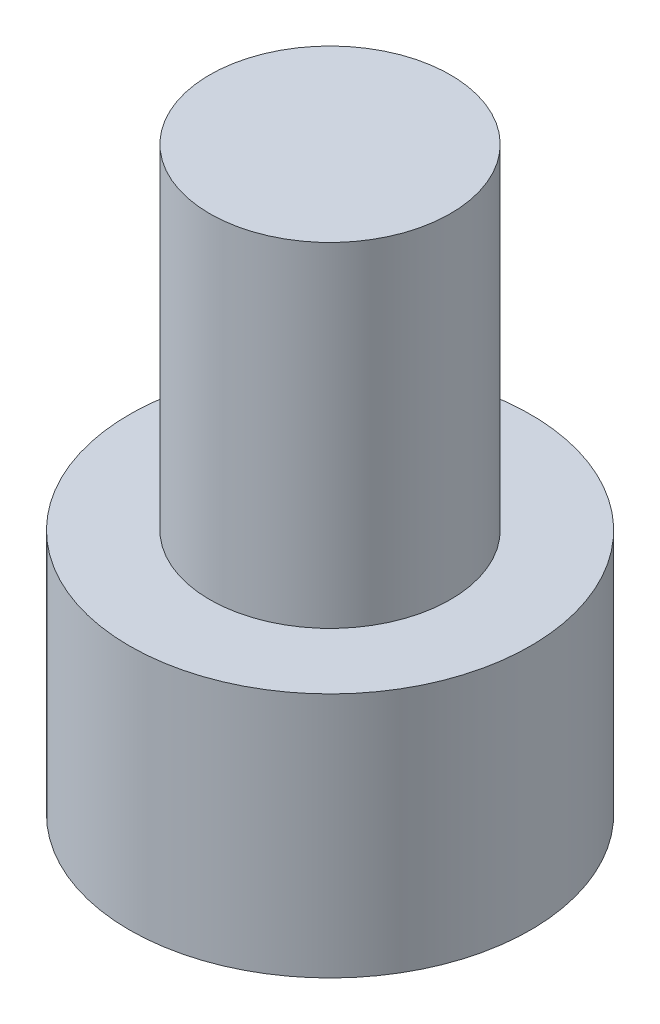
SolidWorks part; units mm, degrees
ref_plane "Front Plane" through (0, 0, 0) normal (0, 0, 1) x (1, 0, 0)
ref_plane "Top Plane" through (0, 0, 0) normal (0, 1, 0) x (1, 0, 0)
ref_plane "Right Plane" through (0, 0, 0) normal (1, 0, 0) x (0, 0, -1)
sketch "Sketch1" plane through (0, 0, 0) normal (0, 1, 0) x (1, 0, 0)
  circle A0 centre (0, 0) radius 2.8575
  dimension "D1" = 5.715
extrude "Boss-Extrude1" add sketch "Sketch1" along normal blind 3.5052
sketch "Sketch2" plane through (0, 0, 0) normal (0, -1, 0) x (1, 0, 0)
  line L1 (1.604, 0) -> (0.802, 1.3891)
  line L2 (0.802, 1.3891) -> (-0.802, 1.3891)
  line L3 (-0.802, 1.3891) -> (-1.604, 0)
  line L4 (-1.604, 0) -> (-0.802, -1.3891)
  line L5 (-0.802, -1.3891) -> (0.802, -1.3891)
  line L6 (0.802, -1.3891) -> (1.604, 0)
  circle A0 centre (0, 0) radius 1.3891 construction
  dimension "D1" = 2.7781
extrude "Cut-Extrude1" cut sketch "Sketch2" against normal blind 1.9558
sketch "Sketch3" plane through (0, 3.5052, 0) normal (0, 1, 0) x (1, 0, 0)
  circle A0 centre (0, 0) radius 1.7145
  dimension "D1" = 3.429
extrude "Boss-Extrude2" add sketch "Sketch3" along normal blind 4.7625
